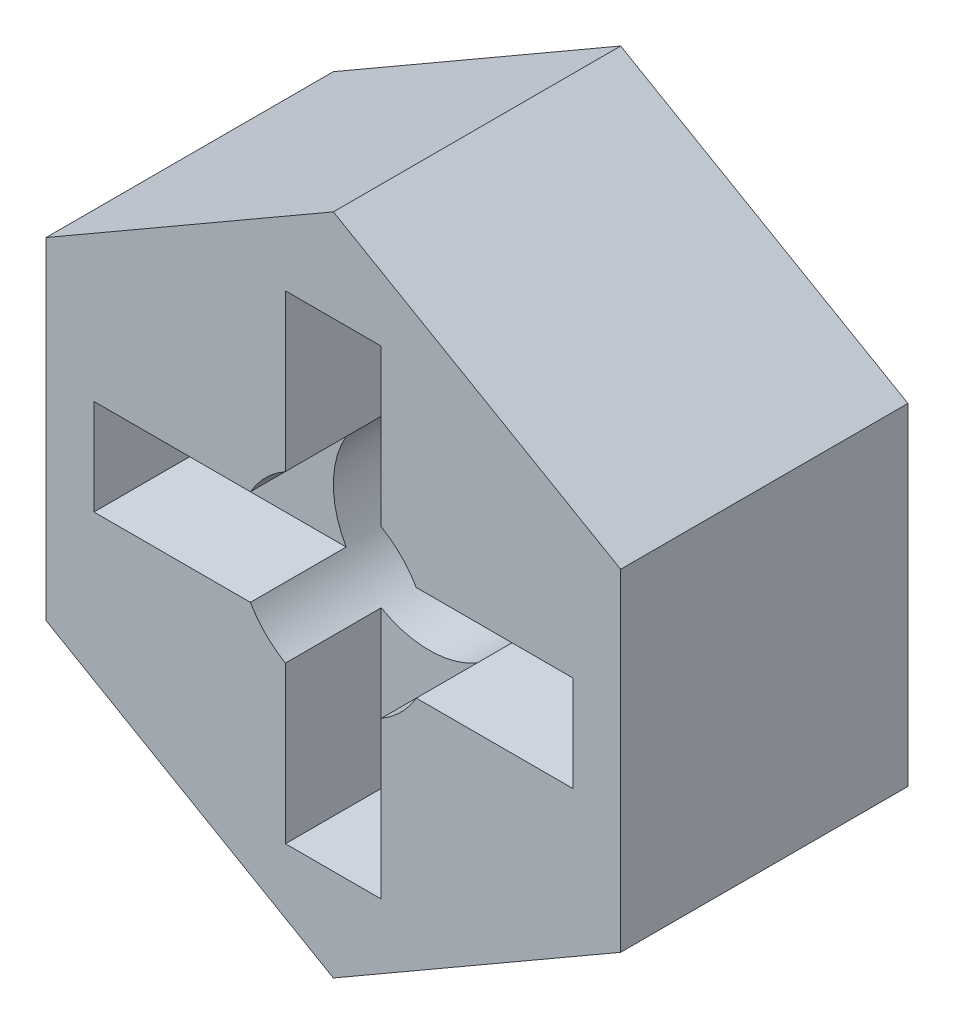
SolidWorks part; units mm, degrees
ref_plane "Plane1" through (0, 0, 0) normal (0, 0, 1) x (1, 0, 0)
ref_plane "Plane2" through (0, 0, 0) normal (0, 1, 0) x (1, 0, 0)
ref_plane "Plane3" through (0, 0, 0) normal (1, 0, 0) x (0, 0, -1)
sketch "Esquisse1" plane through (0, 0, 0) normal (0, 0, 1) x (1, 0, 0)
  line L1 (0, 6.9282) -> (-6, 3.4641)
  line L2 (-6, 3.4641) -> (-6, -3.4641)
  line L3 (-6, -3.4641) -> (0, -6.9282)
  line L4 (0, -6.9282) -> (6, -3.4641)
  line L5 (6, -3.4641) -> (6, 3.4641)
  line L6 (6, 3.4641) -> (0, 6.9282)
  circle A0 centre (0, 0) radius 6 construction
  circle A1 centre (0, 0) radius 2
  dimension "D2" = 4
  dimension "D1" = 12
extrude "Base-Extrusion" add sketch "Esquisse1" along normal blind 6
sketch "Esquisse2" plane through (0, 0, 6) normal (0, 0, 1) x (1, 0, 0)
  line L0 (0, 0) -> (0, 5) construction
  line L1 (1, 5) -> (-1, 5)
  line L2 (-1, 5) -> (-1, 1)
  line L3 (1, 5) -> (1, 1)
  line L4 (1, -1) -> (-1, -1)
  line L5 (5, -1) -> (1, -1)
  line L6 (5, -1) -> (5, 1)
  line L7 (5, 1) -> (1, 1)
  line L8 (-1, -1) -> (-1, 1)
  line L9 (-1, -5) -> (-1, -1)
  line L10 (-1, -5) -> (1, -5)
  line L11 (1, -5) -> (1, -1)
  line L12 (-1, 5) -> (-1, 1)
  line L13 (-5, 1) -> (-1, 1)
  line L14 (-5, 1) -> (-5, -1)
  line L15 (-5, -1) -> (-1, -1)
  line L16 (-1, 1) -> (0, 1)
  line L17 (1, 1) -> (1, -1)
  line L18 (1, 5) -> (1, 1)
  dimension "D1" = 5
extrude "Enlèv. mat.-Extru.1" cut sketch "Esquisse2" against normal blind 2
sketch "Esquisse3" plane through (0, 0, 0) normal (0, 0, -1) x (-1, 0, 0)
  circle A0 centre (0, 0) radius 4
  circle A1 centre (0, 0) radius 5
extrude "Enlèv. mat.-Extru.2" cut sketch "Esquisse3" against normal blind 2
